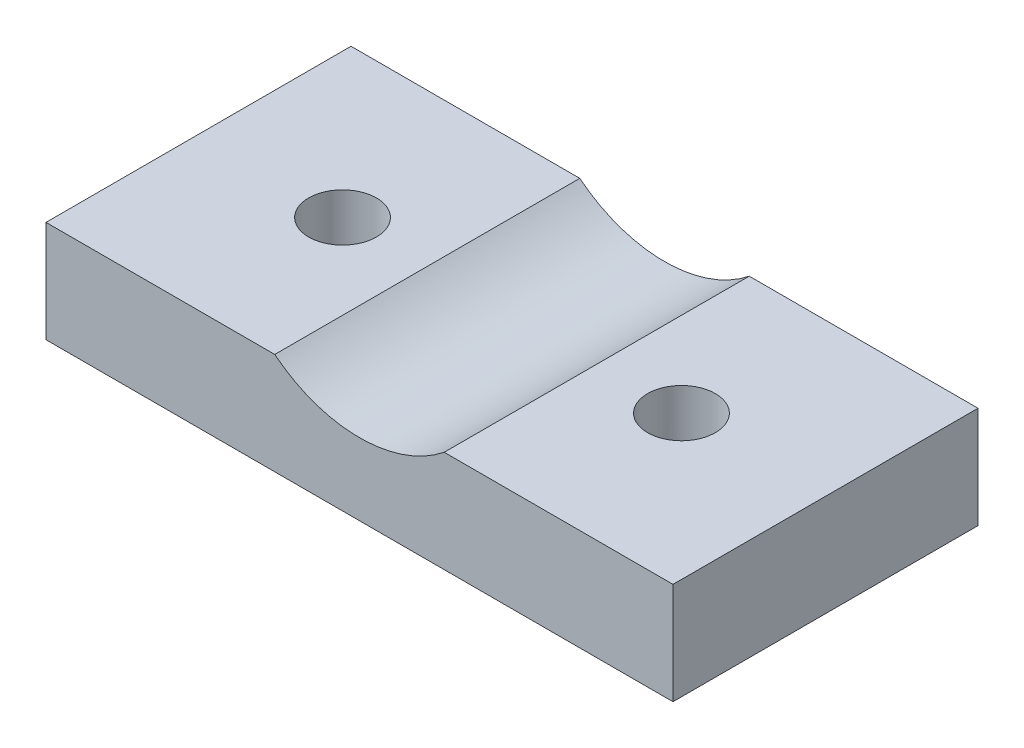
SolidWorks part; units mm, degrees
ref_plane "Front" through (0, 0, 0) normal (0, 0, 1) x (1, 0, 0)
ref_plane "Top" through (0, 0, 0) normal (0, 1, 0) x (1, 0, 0)
ref_plane "Right" through (0, 0, 0) normal (1, 0, 0) x (0, 0, -1)
sketch "Sketch1" plane through (0, 0, 0) normal (0, 0, 1) x (1, 0, 0)
  line L0 (10, 6) -> (37, 6)
  line L1 (-37, 6) -> (-10, 6)
  line L2 (-37, 6) -> (-37, -6)
  line L3 (-37, -6) -> (37, -6)
  line L4 (37, 6) -> (37, -6)
  line L5 (-37, 6) -> (37, -6) construction
  line L6 (-37, -6) -> (37, 6) construction
  arc A0 (-10, 6) -> (10, 6) centre (0, 18.49) ccw
  point P0 (0, 0)
  point P6 (10, 6)
  point P7 (-10, 6)
  dimension "D5" = 16
  dimension "D1" = 74
  dimension "D2" = 12
  dimension "D3" = 10
  dimension "D4" = 10
extrude "Boss-Extrude1" add sketch "Sketch1" against normal blind 36
sketch "Sketch2" plane through (0, 0, 0) normal (0, 1, 0) x (1, 0, 0)
  line L0 (-10, 36) -> (-37, 36) construction
  line L1 (-37, 36) -> (-37, 0) construction
  line L2 (0, 43.1896) -> (0, -12.1696) construction
  circle A0 centre (-20, 18) radius 4
  circle A1 centre (20, 18) radius 4
  dimension "D1" = 8
  dimension "D2" = 18
  dimension "D3" = 17
extrude "Cut-Extrude1" cut sketch "Sketch2" along normal through all
sketch "Sketch3" plane through (0, 0, 0) normal (0, 1, 0) x (1, 0, 0)
  circle A0 centre (-20, 18) radius 4
  circle A1 centre (20, 18) radius 4
extrude "Cut-Extrude2" cut sketch "Sketch3" against normal through all
